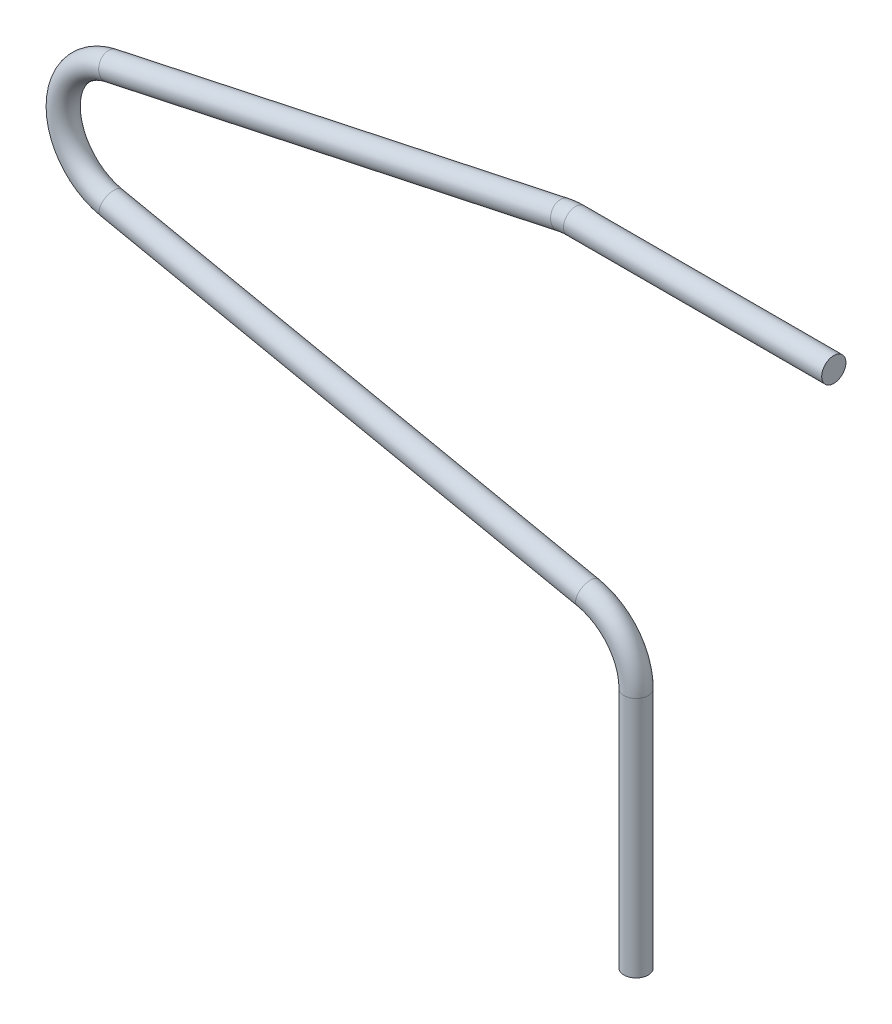
SolidWorks part; units mm, degrees
ref_plane "Vorne" through (0, 0, 0) normal (0, 0, 1) x (1, 0, 0)
ref_plane "Oben" through (0, 0, 0) normal (0, 1, 0) x (1, 0, 0)
ref_plane "Rechts" through (0, 0, 0) normal (1, 0, 0) x (0, 0, -1)
sketch "Skizze1" plane through (0, 0, 0) normal (0, 0, 1) x (1, 0, 0)
  line L0 (0, 0) -> (0, 15)
  line L1 (-2.9845, 18.671) -> (-32.5155, 24.829)
  line L2 (-32.5357, 32.1668) -> (-4.5357, 38.1668)
  line L3 (-3.75, 38.25) -> (12.25, 38.25)
  line L4 (-31.75, 25.5) -> (-3.75, 25.5) construction
  line L5 (-3.75, 25.5) -> (-3.75, 18) construction
  line L6 (-31.75, 31.5) -> (-31.75, 37.5) construction
  line L7 (-31.75, 37.5) -> (-3.75, 37.5) construction
  arc A0 (0, 15) -> (-2.9845, 18.671) centre (-3.75, 15) ccw
  arc A1 (-32.5155, 24.829) -> (-32.5357, 32.1668) centre (-31.75, 28.5) cw
  arc A2 (-4.5357, 38.1668) -> (-3.75, 38.25) centre (-3.75, 34.5) cw
  circle A3 centre (-31.75, 28.5) radius 3.75 construction
  circle A4 centre (-3.75, 34.5) radius 3.75 construction
  circle A5 centre (-3.75, 15) radius 3.75 construction
  circle A6 centre (-31.75, 28.5) radius 3 construction
  circle A7 centre (-3.75, 15) radius 3 construction
  circle A8 centre (-3.75, 34.5) radius 3 construction
  dimension "D1" = 6
  dimension "D2" = 6
  dimension "D3" = 7.5
  dimension "D7" = 6
  dimension "D8" = 7.5
  dimension "D4" = 28
  dimension "D5" = 15
  dimension "D6" = 16
  dimension "D9" = 6
sketch "Skizze2" plane through (0, 0, 0) normal (0, 1, 0) x (1, 0, 0)
  circle A0 centre (0, 0) radius 0.75
  dimension "D1" = 1.5
sweep "Austragung1" add profiles "Skizze2" path "Skizze1"
move or copy body "Körper-Verschieben/Kopieren1" [suppressed] bodies to move or copy 103
